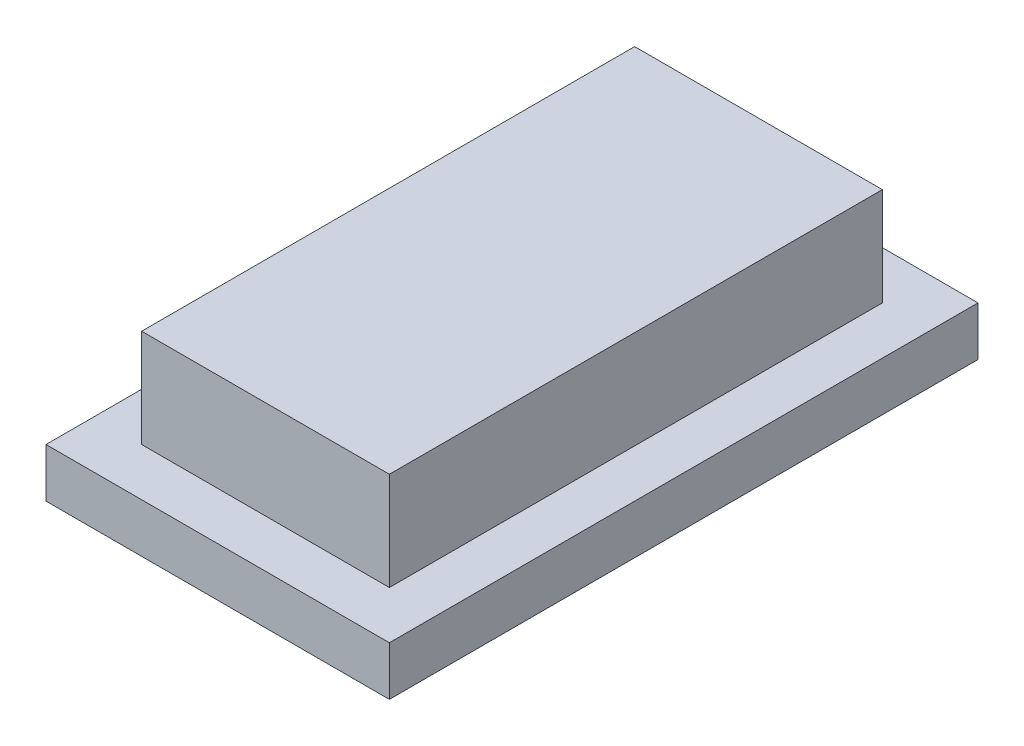
SolidWorks part; units mm, degrees
ref_plane "Спереди" through (0, 0, 0) normal (0, 0, 1) x (1, 0, 0)
ref_plane "Сверху" through (0, 0, 0) normal (0, 1, 0) x (1, 0, 0)
ref_plane "Справа" through (0, 0, 0) normal (1, 0, 0) x (0, 0, -1)
sketch "Sketch1" plane through (0, 0, 0) normal (0, 1, 0) x (1, 0, 0)
  line L1 (7, -12) -> (-7, -12)
  line L2 (7, -12) -> (7, 12)
  line L3 (7, 12) -> (-7, 12)
  line L4 (-7, -12) -> (-7, 12)
  line L5 (7, -12) -> (-7, 12) construction
  line L6 (7, 12) -> (-7, -12) construction
  point P0 (0, 0)
  dimension "D1" = 14
  dimension "D2" = 24
extrude "Boss-Extrude1" add sketch "Sketch1" along normal blind 2
sketch "Sketch2" plane through (0, 2, 0) normal (0, 1, 0) x (1, 0, 0)
  line L1 (5.05, -10.05) -> (-5.05, -10.05)
  line L2 (5.05, -10.05) -> (5.05, 10.05)
  line L3 (5.05, 10.05) -> (-5.05, 10.05)
  line L4 (-5.05, -10.05) -> (-5.05, 10.05)
  line L5 (5.05, -10.05) -> (-5.05, 10.05) construction
  line L6 (5.05, 10.05) -> (-5.05, -10.05) construction
  point P0 (0, 0)
  dimension "D1" = 10.1
  dimension "D2" = 20.1
extrude "Boss-Extrude2" add sketch "Sketch2" along normal blind 4
